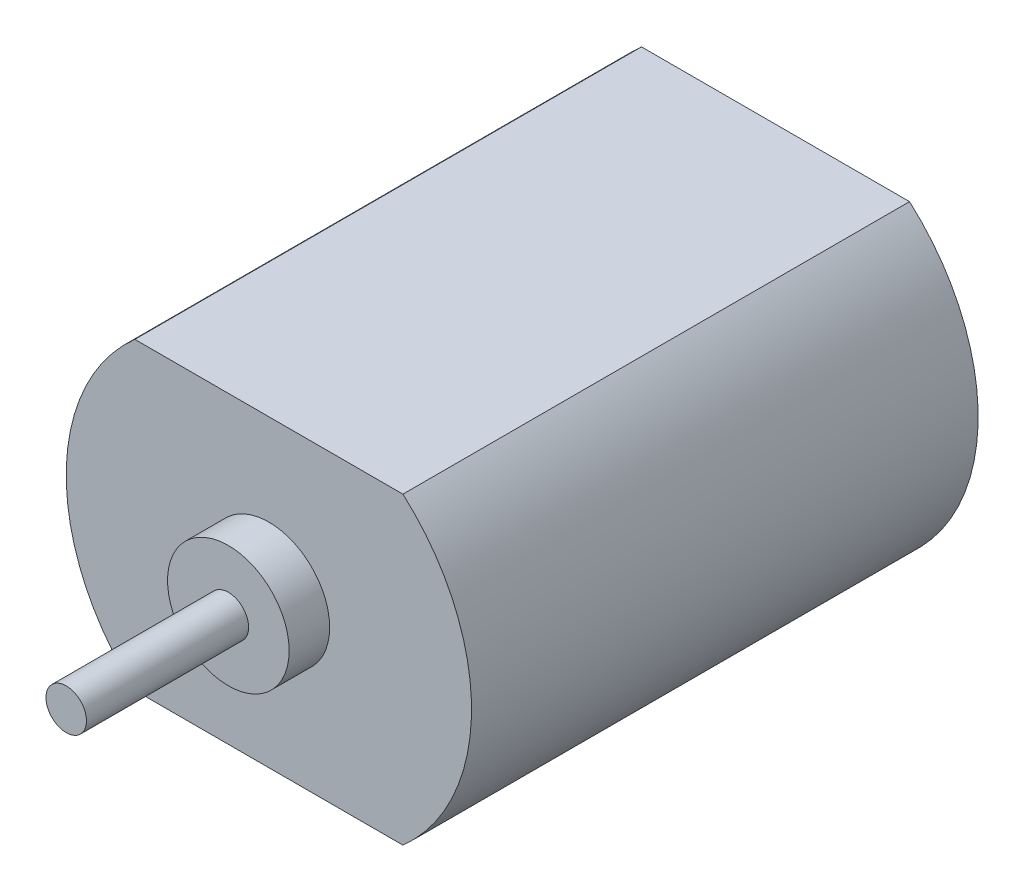
SolidWorks part; units mm, degrees
ref_plane "Plan de face" through (0, 0, 0) normal (0, 0, 1) x (1, 0, 0)
ref_plane "Plan de dessus" through (0, 0, 0) normal (0, 1, 0) x (1, 0, 0)
ref_plane "Plan de droite" through (0, 0, 0) normal (1, 0, 0) x (0, 0, -1)
sketch "Esquisse1" plane through (0, 0, 0) normal (0, 0, 1) x (1, 0, 0)
  line L0 (-6.6144, 7.5) -> (6.6144, 7.5)
  line L1 (-6.6144, -7.5) -> (6.6144, -7.5)
  arc A0 (-6.6144, 7.5) -> (-6.6144, -7.5) centre (0, 0) ccw
  arc A1 (6.6144, -7.5) -> (6.6144, 7.5) centre (0, 0) ccw
  dimension "D1" = 20
  dimension "D2" = 15
  dimension "D3" = 7.5
extrude "Boss.-Extru.1" add sketch "Esquisse1" along normal blind 25
sketch "Esquisse2" plane through (0, 0, 25) normal (0, 0, 1) x (1, 0, 0)
  circle A0 centre (0, 0) radius 3
  dimension "D1" = 6
extrude "Boss.-Extru.2" add sketch "Esquisse2" along normal blind 2
sketch "Esquisse3" plane through (0, 0, 27) normal (0, 0, 1) x (1, 0, 0)
  circle A0 centre (0, 0) radius 1
  dimension "D1" = 2
extrude "Boss.-Extru.3" add sketch "Esquisse3" along normal blind 8
